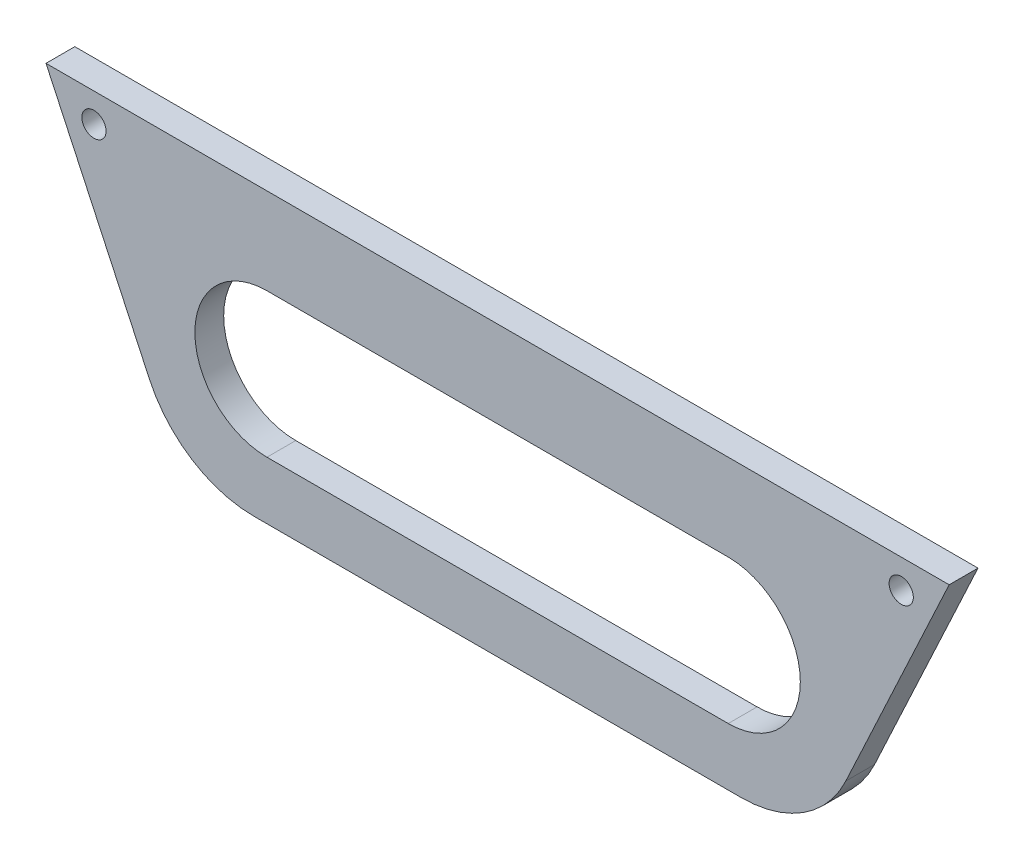
SolidWorks part; units mm, degrees
ref_plane "Front Plane" through (0, 0, 0) normal (0, 0, 1) x (1, 0, 0)
ref_plane "Top Plane" through (0, 0, 0) normal (0, 1, 0) x (1, 0, 0)
ref_plane "Right Plane" through (0, 0, 0) normal (1, 0, 0) x (0, 0, -1)
sketch "Sketch1" plane through (0, 0, 0) normal (0, 0, 1) x (1, 0, 0)
  line L0 (156.6308, 0) -> (0, 0)
  line L4 (118.3154, -15) -> (38.3154, -15)
  line L5 (38.3154, -40) -> (118.3154, -40)
  line L56 (0, 0) -> (17.9306, -38.4524)
  line L57 (36.0568, -50) -> (120.574, -50)
  line L58 (138.7001, -38.4524) -> (156.6308, 0)
  arc A4 (17.9306, -38.4524) -> (36.0568, -50) centre (36.0568, -30) ccw
  arc A5 (120.574, -50) -> (138.7001, -38.4524) centre (120.574, -30) ccw
  arc A6 (118.3154, -40) -> (118.3154, -15) centre (118.3154, -27.5) ccw
  arc A7 (38.3154, -15) -> (38.3154, -40) centre (38.3154, -27.5) ccw
  circle A18 centre (148.3154, -5) radius 2.1
  circle A19 centre (8.3154, -5) radius 2.1
  dimension "D1" = 4.2
  dimension "D2" = 20
  dimension "D3" = 12.5
  dimension "D4" = 8.3154
  dimension "D5" = 17.9306
  dimension "D6" = 36.0568
  dimension "D7" = 38.3154
  dimension "D8" = 118.3154
  dimension "D9" = 120.574
  dimension "D10" = 148.3154
  dimension "D11" = 5
  dimension "D12" = 27.5
extrude "Boss-Extrude1" add sketch "Sketch1" along normal blind 5
